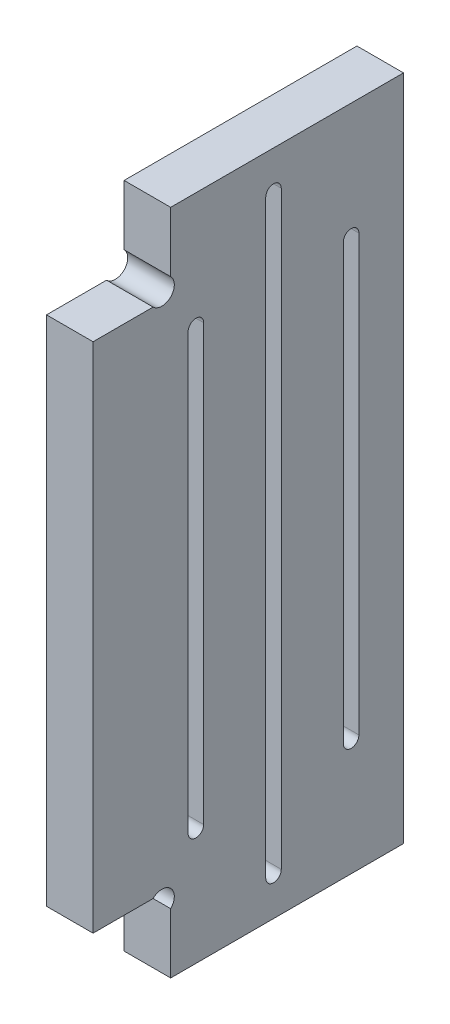
SolidWorks part; units mm, degrees
ref_plane "Plan de face" through (0, 0, 0) normal (0, 0, 1) x (1, 0, 0)
ref_plane "Plan de dessus" through (0, 0, 0) normal (0, 1, 0) x (1, 0, 0)
ref_plane "Plan de droite" through (0, 0, 0) normal (1, 0, 0) x (0, 0, -1)
sketch "Esquisse1" plane through (0, 0, 0) normal (1, 0, 0) x (0, 0, -1)
  line L4 (110, 226.8628) -> (80, 226.8628)
  line L6 (77.7373, 150.8628) -> (70, 150.8628)
  line L8 (77.7373, 216.8628) -> (70, 216.8628)
  line L9 (80, 140.8628) -> (80, 148.6001)
  line L12 (70, 150.8628) -> (70, 216.8628)
  line L13 (80, 219.1256) -> (80, 226.8628)
  line L46 (80, 140.8628) -> (110, 140.8628)
  line L49 (110, 140.8628) -> (110, 226.8628)
  arc A0 (80, 148.6001) -> (77.7373, 150.8628) centre (78.8686, 149.7315) ccw
  arc A1 (80, 219.1256) -> (77.7373, 216.8628) centre (78.8686, 217.9942) cw
  dimension "D4" = 10
  dimension "D12" = 30
  dimension "D7" = 8.8686
  dimension "D9" = 86
  dimension "D11" = 1.6
  dimension "D2" = 1.6
  dimension "D3" = 10
  dimension "D5" = 10
  dimension "D6" = 8.8686
  dimension "D8" = 8.8686
  dimension "D10" = 10
extrude "Extrusion1" add sketch "Esquisse1" along normal blind 6
sketch "Esquisse3" plane through (0, 0, 0) normal (-1, 0, 0) x (0, 0, 1)
  line L0 (-83.25, 155.8628) -> (-83.25, 211.8628) construction
  line L1 (-84.25, 155.8628) -> (-84.25, 211.8628)
  line L2 (-82.25, 155.8628) -> (-82.25, 211.8628)
  line L3 (-93.25, 145.8628) -> (-93.25, 221.8628) construction
  line L4 (-94.25, 145.8628) -> (-94.25, 221.8628)
  line L5 (-92.25, 145.8628) -> (-92.25, 221.8628)
  line L6 (-103.25, 155.8628) -> (-103.25, 211.8628) construction
  line L7 (-104.25, 155.8628) -> (-104.25, 211.8628)
  line L8 (-102.25, 155.8628) -> (-102.25, 211.8628)
  line L9 (-80, 140.8628) -> (-110, 140.8628) construction
  line L10 (-110, 226.8628) -> (-80, 226.8628) construction
  line L11 (-80, 148.6001) -> (-80, 140.8628) construction
  arc A0 (-84.25, 155.8628) -> (-82.25, 155.8628) centre (-83.25, 155.8628) ccw
  arc A1 (-82.25, 211.8628) -> (-84.25, 211.8628) centre (-83.25, 211.8628) ccw
  arc A2 (-94.25, 145.8628) -> (-92.25, 145.8628) centre (-93.25, 145.8628) ccw
  arc A3 (-92.25, 221.8628) -> (-94.25, 221.8628) centre (-93.25, 221.8628) ccw
  arc A4 (-104.25, 155.8628) -> (-102.25, 155.8628) centre (-103.25, 155.8628) ccw
  arc A5 (-102.25, 211.8628) -> (-104.25, 211.8628) centre (-103.25, 211.8628) ccw
  point P2 (-83.25, 183.8628)
  point P7 (-93.25, 183.8628)
  point P14 (-103.25, 183.8628)
  dimension "D1" = 1
  dimension "D2" = 1
  dimension "D3" = 1
  dimension "D4" = 15
  dimension "D5" = 15
  dimension "D6" = 3.25
  dimension "D7" = 10
  dimension "D8" = 10
  dimension "D9" = 5
  dimension "D10" = 5
extrude "Enlèv. mat.-Extru.2" cut sketch "Esquisse3" against normal through all
